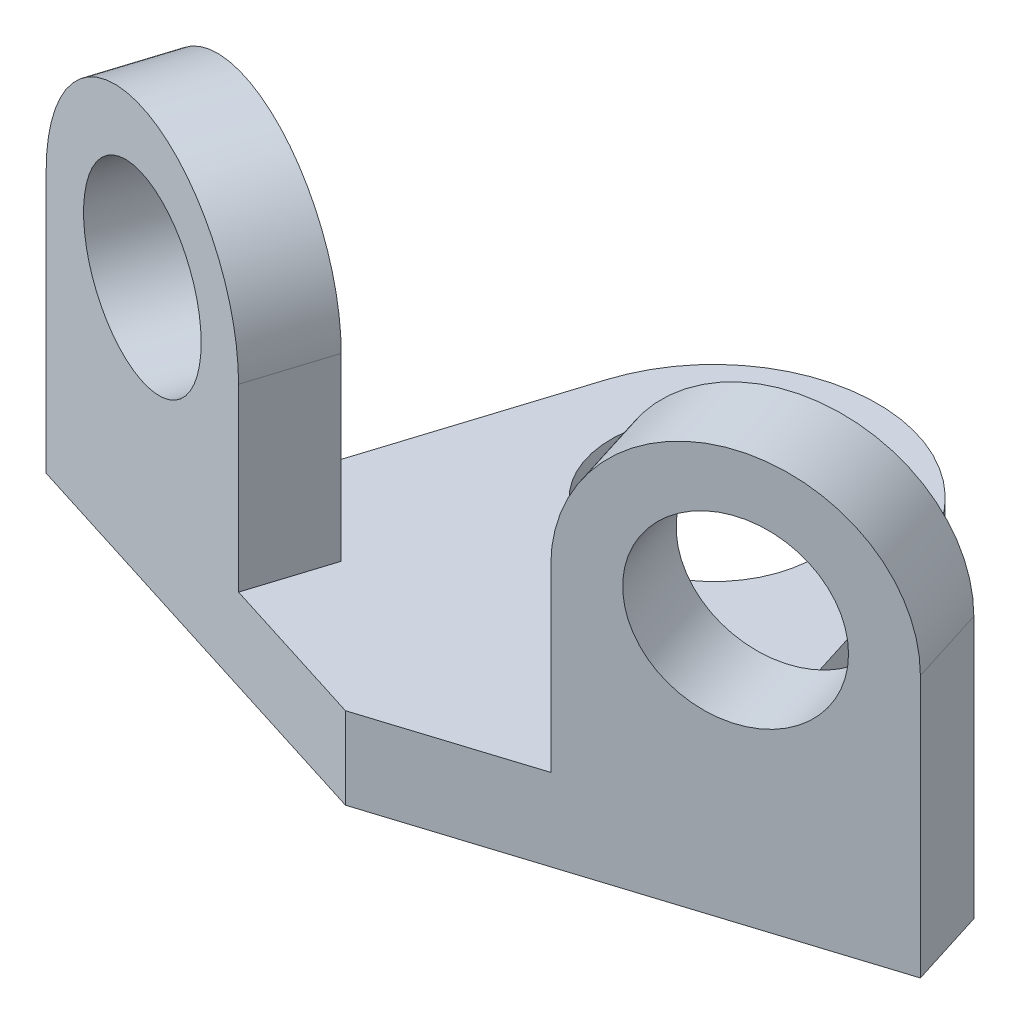
SolidWorks part; units mm, degrees
material "Cast Carbon Steel"
ref_plane "Front Plane" through (0, 0, 0) normal (0, 0, 1) x (1, 0, 0)
ref_plane "Top Plane" through (0, 0, 0) normal (0, 1, 0) x (1, 0, 0)
ref_plane "Right Plane" through (0, 0, 0) normal (1, 0, 0) x (0, 0, -1)
sketch "Sketch1" plane through (0, 0, 0) normal (0, 1, 0) x (1, 0, 0)
  line L0 (0, 0) -> (53.4081, 16.8395)
  line L1 (53.4081, 16.8395) -> (0, 0)
  line L2 (0, 0) -> (-53.4081, 16.8395)
  line L3 (0, 0) -> (0, -31.3454) construction
  line L4 (53.4081, 16.8395) -> (50.4011, 26.3767)
  line L5 (50.4011, 26.3767) -> (28.9728, 19.6204)
  line L6 (-50.4011, 26.3767) -> (-28.9728, 19.6204)
  line L7 (-53.4081, 16.8395) -> (-50.4011, 26.3767)
  line L8 (-28.9728, 19.6204) -> (-19.0743, 51.0141)
  line L9 (28.9728, 19.6204) -> (19.0743, 51.0141)
  arc A2 (19.0743, 51.0141) -> (-19.0743, 51.0141) centre (0, 45) ccw
  circle A3 centre (0, 45) radius 12.5
  dimension "D1" = 40
  dimension "D2" = 25
  dimension "D3" = 45
  dimension "D4" = 56
  dimension "D5" = 35
  dimension "D7" = 10
  dimension "D8" = 10
extrude "Boss-Extrude1" add sketch "Sketch1" along normal blind 10
sketch "Sketch2" plane through (0, 0, 0) normal (0.3007, 0, 0.9537) x (0.9537, 0, -0.3007)
  line L0 (56, 32) -> (56, 10)
  line L1 (0, 10) -> (56, 10) construction
  line L2 (56, 10) -> (56, 0) construction
  line L3 (20, 32) -> (20, 10)
  line L4 (20, 10) -> (56, 10)
  line L5 (0, 0) -> (56, 0) construction
  arc A0 (56, 32) -> (20, 32) centre (38, 32) ccw
  circle A1 centre (38, 32) radius 11
  dimension "D1" = 36
  dimension "D2" = 22
  dimension "D3" = 32
extrude "Boss-Extrude2" add sketch "Sketch2" against normal up to surface (10 mm away) up to face at (39.6869, 5, -22.9985)
sketch "Sketch4" plane through (0, 0, 0) normal (-0.3007, 0, 0.9537) x (0.9537, 0, 0.3007)
  line L0 (-20, 32) -> (-20, 10)
  line L1 (-56, 32) -> (-56, 10)
  line L2 (-56, 10) -> (-20, 10)
  line L4 (0, 0) -> (-56, 0) construction
  line L7 (-56, 0) -> (0, 0)
  line L8 (0, 0) -> (0, 10)
  line L9 (0, 10) -> (-56, 10)
  line L10 (-56, 10) -> (-56, 0)
  line L13 (-20, 10) -> (-56, 10)
  arc A0 (-20, 32) -> (-56, 32) centre (-38, 32) ccw
  circle A1 centre (-38, 32) radius 11
  line M9 (0, 10) -> (-56, 10)
  dimension "D1" = 36
  dimension "D2" = 22
  dimension "D3" = 32
  dimension "D4" = 0
extrude "Boss-Extrude3" add sketch "Sketch4" against normal up to surface (10 mm away) contours L0 A0 L1 A1 M9 up to face at (-39.6869, 5, -22.9985)
